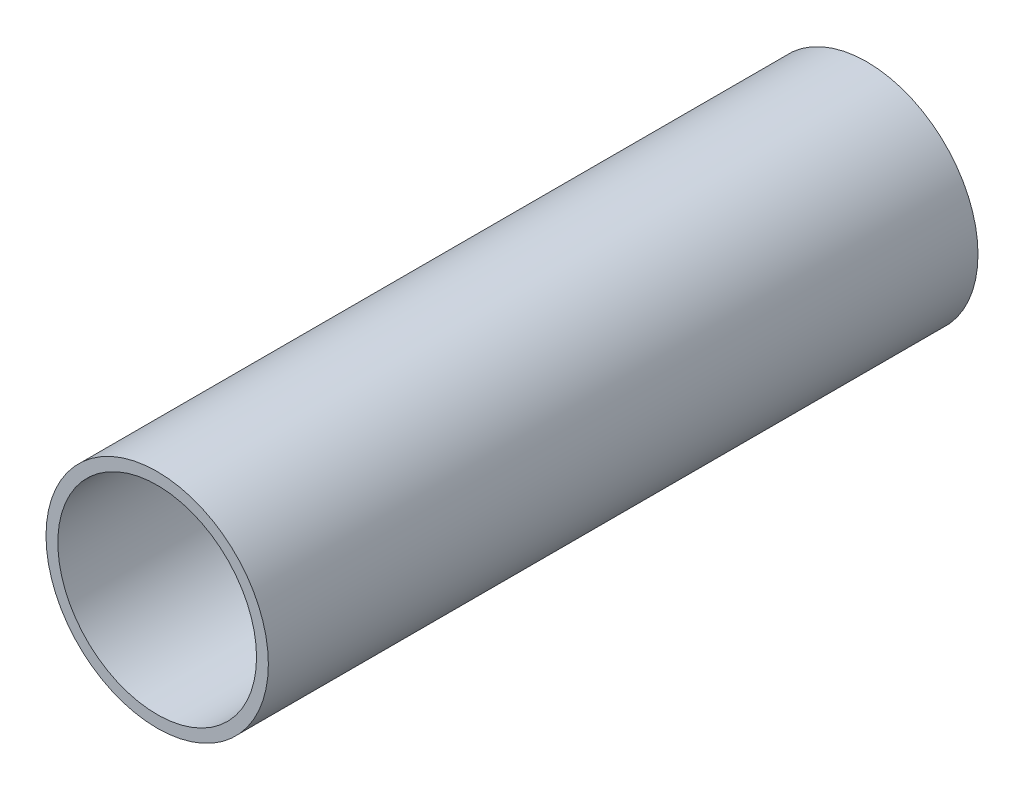
SolidWorks part; units mm, degrees
material "AISI Type 316L stainless steel"
ref_plane "Front Plane" through (0, 0, 0) normal (0, 0, 1) x (1, 0, 0)
ref_plane "Top Plane" through (0, 0, 0) normal (0, 1, 0) x (1, 0, 0)
ref_plane "Right Plane" through (0, 0, 0) normal (1, 0, 0) x (0, 0, -1)
sketch "Sketch1" plane through (0, 0, 0) normal (0, 0, 1) x (1, 0, 0)
  circle A0 centre (0, 0) radius 5.969
  dimension "D1" = 11.938
extrude "Boss-Extrude1" add sketch "Sketch1" along normal blind 38.1
sketch "Sketch2" plane through (0, 0, 38.1) normal (0, 0, 1) x (1, 0, 0)
  circle A0 centre (0, 0) radius 5.334
  dimension "D1" = 10.668
extrude "Cut-Extrude1" cut sketch "Sketch2" against normal blind 38.1
